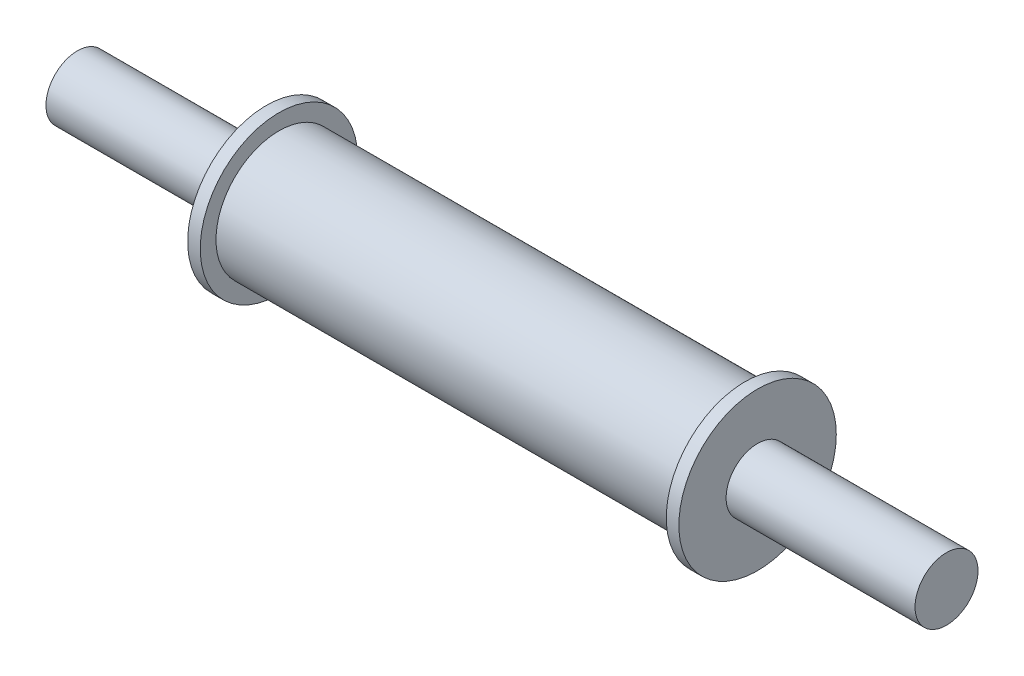
SolidWorks part; units mm, degrees
ref_plane "Front Plane" through (0, 0, 0) normal (0, 0, 1) x (1, 0, 0)
ref_plane "Top Plane" through (0, 0, 0) normal (0, 1, 0) x (1, 0, 0)
ref_plane "Right Plane" through (0, 0, 0) normal (1, 0, 0) x (0, 0, -1)
sketch "Sketch1" plane through (0, 0, 0) normal (1, 0, 0) x (0, 0, -1)
  circle A0 centre (0, 0) radius 10
  dimension "D1" = 20
extrude "Boss-Extrude1" add sketch "Sketch1" along normal blind 37
sketch "Sketch2" plane through (37, 0, 0) normal (1, 0, 0) x (0, 0, -1)
  circle A0 centre (0, 0) radius 12.5
  dimension "D1" = 25
extrude "Boss-Extrude2" add sketch "Sketch2" along normal blind 2
sketch "Sketch3" plane through (39, 0, 0) normal (1, 0, 0) x (0, 0, -1)
  circle A0 centre (0, 0) radius 5
  dimension "D1" = 10
extrude "Boss-Extrude3" add sketch "Sketch3" along normal blind 30
mirror "Mirror2" about plane through (0, 0, 0) normal (1, 0, 0) of "Boss-Extrude3", "Boss-Extrude2", "Boss-Extrude1"
